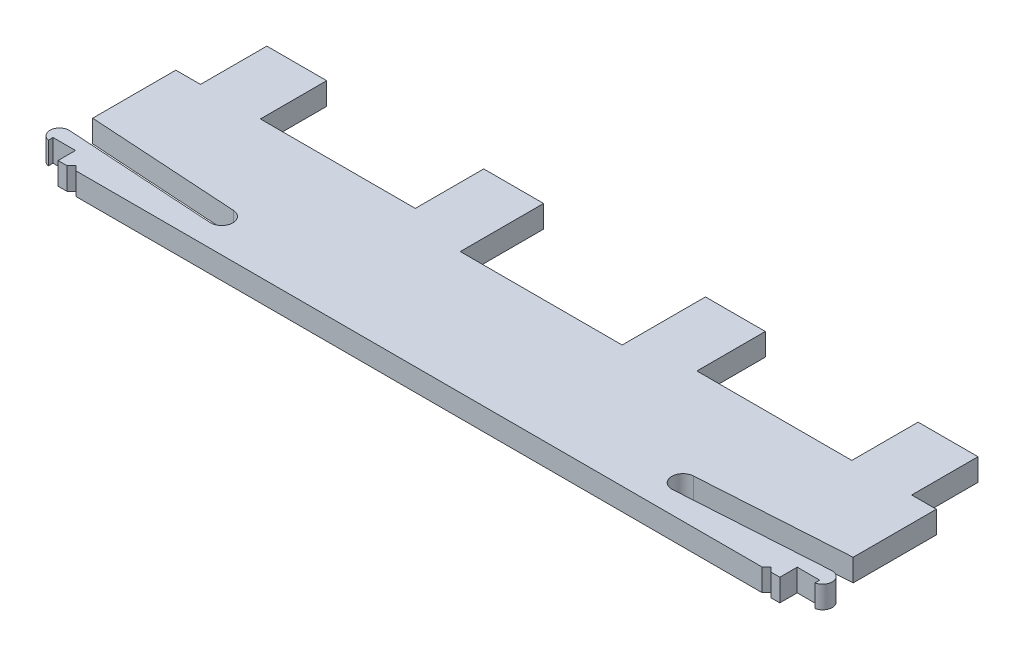
SolidWorks part; units mm, degrees
ref_plane "Front Plane" through (0, 0, 0) normal (0, 0, 1) x (1, 0, 0)
ref_plane "Top Plane" through (0, 0, 0) normal (0, 1, 0) x (1, 0, 0)
ref_plane "Right Plane" through (0, 0, 0) normal (1, 0, 0) x (0, 0, -1)
sketch "Sketch1" plane through (0, 0, 0) normal (0, 1, 0) x (1, 0, 0)
  line L0 (2.0552, 14.547) -> (2.0552, 5.724)
  line L1 (-0.9565, 0) -> (-1.4366, 0.4801)
  line L2 (-1.4366, 0.4801) -> (-1.9167, 0)
  line L3 (-23.3448, 14.547) -> (-6.911, 14.547)
  line L4 (-23.3448, 14.547) -> (-23.3448, 21.8063)
  line L5 (-23.3448, 21.8063) -> (-29.6948, 21.8063)
  line L6 (-29.6948, 21.8063) -> (-29.6948, 12.9671)
  line L7 (-29.6948, 12.9671) -> (-46.8652, 12.9671)
  line L8 (0, 0) -> (-0.9565, 0)
  line L9 (-38.28, 0) -> (-38.28, 12.9671) construction
  line L10 (2.0552, 4.5406) -> (-13.8198, 3.541) construction
  line L11 (2.1294, 3.3618) -> (-13.7456, 2.3622) construction
  line L12 (1.981, 5.7193) -> (-13.894, 4.7197) construction
  line L13 (2.0552, 5.724) -> (-13.894, 4.7197)
  line L14 (2.1294, 3.3618) -> (-13.7456, 2.3622)
  line L15 (2.3876, 1.3506) -> (2.3876, 1.8465)
  line L16 (2.3876, 1.8465) -> (0, 1.8465)
  line L17 (-6.911, 14.547) -> (-6.911, 21.5828)
  line L18 (-6.911, 21.5828) -> (-0.561, 21.5828)
  line L19 (-0.561, 21.5828) -> (-0.561, 14.547)
  line L20 (-0.561, 14.547) -> (2.0552, 14.547)
  line L21 (0, 1.8465) -> (0, 0)
  line L22 (-76.56, 0) -> (-75.6034, 0)
  line L23 (-75.1234, 0.4801) -> (-74.6433, 0)
  line L24 (-75.6034, 0) -> (-75.1234, 0.4801)
  line L25 (-1.9167, 0) -> (-74.6433, 0)
  line L26 (-76.56, 1.8465) -> (-76.56, 0)
  line L27 (-78.9476, 1.8465) -> (-76.56, 1.8465)
  line L28 (-78.9476, 1.3506) -> (-78.9476, 1.8465)
  line L29 (-78.6894, 3.3618) -> (-62.8144, 2.3622)
  line L30 (-78.6152, 5.724) -> (-62.666, 4.7197)
  line L31 (-78.6152, 14.547) -> (-78.6152, 5.724)
  line L32 (-75.999, 14.547) -> (-78.6152, 14.547)
  line L33 (-75.999, 21.5828) -> (-75.999, 14.547)
  line L34 (-69.649, 21.5828) -> (-75.999, 21.5828)
  line L35 (-53.2152, 14.547) -> (-69.649, 14.547)
  line L36 (-69.649, 14.547) -> (-69.649, 21.5828)
  line L37 (-53.2152, 14.547) -> (-53.2152, 21.8063)
  line L38 (-46.8652, 21.8063) -> (-46.8652, 12.9671)
  line L39 (-53.2152, 21.8063) -> (-46.8652, 21.8063)
  arc A0 (2.1294, 3.3618) -> (2.3876, 1.3506) centre (2.1933, 2.3478) cw
  arc A1 (2.1294, 3.3618) -> (1.981, 5.7193) centre (2.0552, 4.5406) ccw construction
  arc A2 (-13.894, 4.7197) -> (-13.7456, 2.3622) centre (-13.8198, 3.541) ccw construction
  arc A3 (-13.894, 4.7197) -> (-13.7456, 2.3622) centre (-13.8198, 3.541) ccw
  arc A4 (-78.6894, 3.3618) -> (-78.9476, 1.3506) centre (-78.7533, 2.3478) ccw
  arc A5 (-62.666, 4.7197) -> (-62.8144, 2.3622) centre (-62.7402, 3.541) cw
  point P12 (2.0552, 4.5406)
  point P15 (-5.8823, 4.0408)
  dimension "D4" = 1.016
  dimension "D10" = 14.547
  dimension "D16" = 2.3478
  dimension "D1" = 8.8392
  dimension "D2" = 2.6162
  dimension "D3" = 6.35
  dimension "D5" = 7.0358
  dimension "D6" = 25.4
  dimension "D7" = 8.5852
  dimension "D8" = 6.35
  dimension "D9" = 1.1811
  dimension "D11" = 15.875
  dimension "D12" = 0.6789
  dimension "D13" = 2.3876
  dimension "D14" = 0.9565
  dimension "D15" = 1.8465
  dimension "D17" = 0.496
  dimension "D18" = 2.3622
  dimension "D19" = 21.8063
extrude "Boss-Extrude1" add sketch "Sketch1" along normal blind 2.3622
